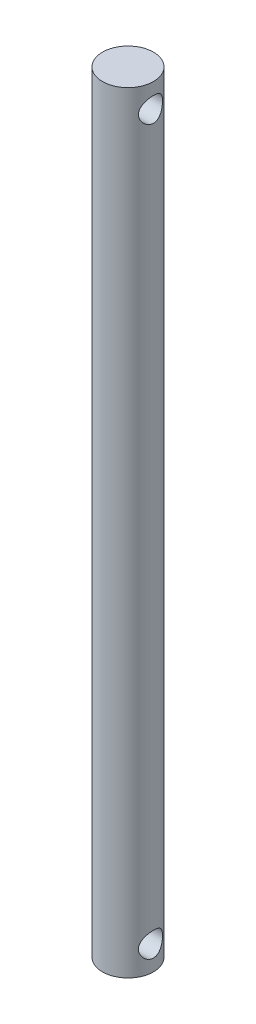
SolidWorks part; units mm, degrees
material "ABS"
ref_plane "Alzado" through (0, 0, 0) normal (0, 0, 1) x (1, 0, 0)
ref_plane "Planta" through (0, 0, 0) normal (0, 1, 0) x (1, 0, 0)
ref_plane "Vista lateral" through (0, 0, 0) normal (1, 0, 0) x (0, 0, -1)
sketch "Croquis1" plane through (0, 0, 0) normal (0, 1, 0) x (1, 0, 0)
  circle A0 centre (0, 0) radius 3.175
  dimension "D1" = 6.35
extrude "Saliente-Extruir1" add sketch "Croquis1" along normal mid plane 96
sketch "Croquis2" plane through (0, 0, 0) normal (1, 0, 0) x (0, 0, -1)
  line L5 (3.175, 48) -> (-3.175, 48) construction
  circle A0 centre (0, 45) radius 1.5
  dimension "D2" = 3
  dimension "D1" = 3
extrude "Cortar-Extruir1" cut sketch "Croquis2" against normal through all both and the other way through all
ref_plane "Plano1" through (-3.175, 0, 0) normal (-1, 0, 0) x (0, 0, 1)
mirror "Simetría3" about plane through (0, 0, 0) normal (0, 1, 0) of "Cortar-Extruir1"
equation "\"g\"= 6.35"
equation "\"D1@Croquis1\"=\"g\""
equation "\"l\"= 90"
equation "\"D1@Saliente-Extruir1\"=\"l\"+\"d\"+\"d\""
equation "\"d\"= 3"
equation "\"D2@Croquis2\"=\"d\""
equation "\"D1@Croquis2\"=\"d\""
